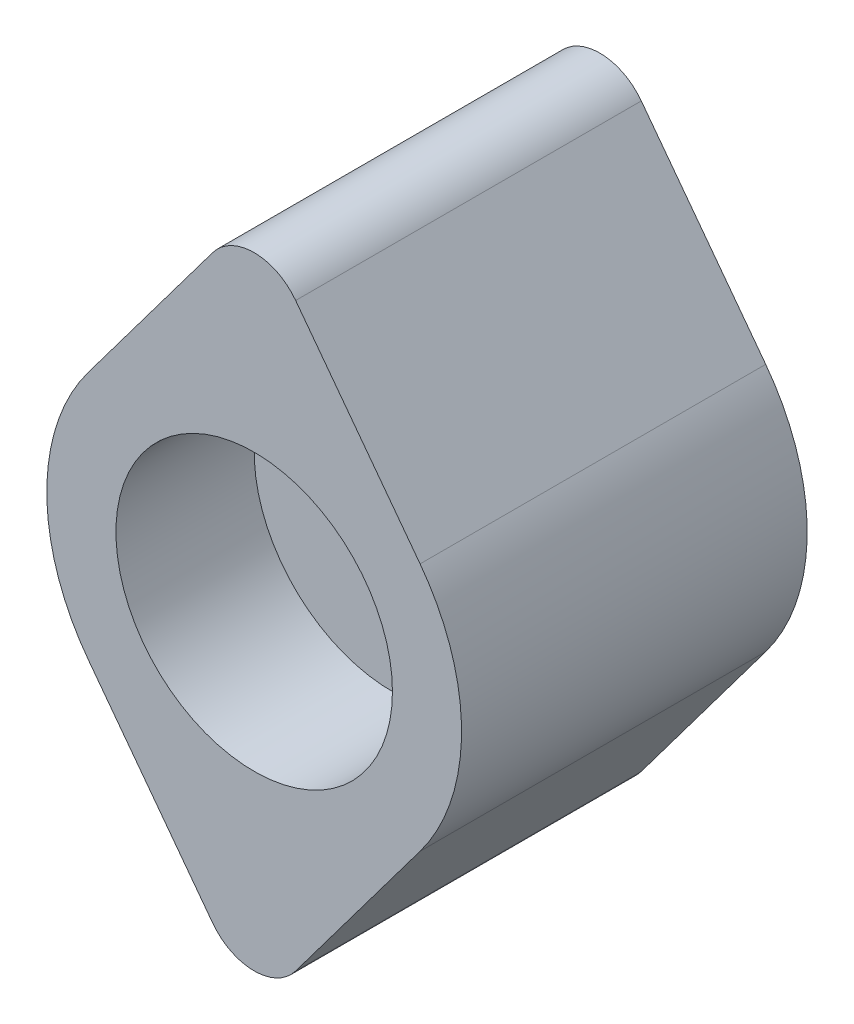
SolidWorks part; units mm, degrees
ref_plane "Спереди" through (0, 0, 0) normal (0, 0, 1) x (1, 0, 0)
ref_plane "Сверху" through (0, 0, 0) normal (0, 1, 0) x (1, 0, 0)
ref_plane "Справа" through (0, 0, 0) normal (1, 0, 0) x (0, 0, -1)
sketch "Эскиз1" plane through (0, 0, 0) normal (0, 0, 1) x (1, 0, 0)
  line L0 (0, 43.4129) -> (0, -56.9191) construction
  line L1 (-52.9224, 0) -> (49.3391, 0) construction
  line L2 (-18.0003, 10) -> (26.0336, 10) construction
  line L3 (-15.5369, -10) -> (30.1599, -10) construction
  line L4 (0, 10) -> (-4.8, 3.6)
  line L5 (0, 10) -> (4.8, 3.6)
  line L6 (0, -10) -> (4.8, -3.6)
  line L7 (0, -10) -> (-4.8, -3.6)
  arc A0 (-4.8, 3.6) -> (-4.8, -3.6) centre (0, 0) ccw
  arc A1 (4.8, -3.6) -> (4.8, 3.6) centre (0, 0) ccw
  dimension "D1" = 12
  dimension "D2" = 10
  dimension "D3" = 10
extrude "Бобышка-Вытянуть1" add sketch "Эскиз1" along normal blind 10
sketch "Эскиз2" plane through (0, 0, 10) normal (0, 0, 1) x (1, 0, 0)
  circle A0 centre (0, 0) radius 4
  dimension "D1" = 8
extrude "Вырез-Вытянуть1" cut sketch "Эскиз2" against normal blind 4
hole_wizard "Отверстие обработанное метчиком M4x0.71" positions "Эскиз4" profile "Эскиз3" tap size "M4x0.7" standard "Ansi Metric" end condition through all
sketch "Эскиз4" plane through (0, 0, 6) normal (0, 0, 1) x (1, 0, 0)
  point P0 (0, 0)
sketch "Эскиз3" plane through (0, 0, 6) normal (1, 0, 0) x (0, -1, 0)
  line L0 (0, 0) -> (0, 6)
  line L1 (0, 6) -> (1.65, 6)
  line L2 (1.65, 6) -> (1.65, 0)
  line L5 (1.65, 0) -> (0, 0)
  line L11 (0, -6.35) -> (0, 107.95) construction
  dimension "Диаметр проходного сверла" = 3.3
  dimension "Глубина проходного сверла" = 6
cosmetic thread "Отверстие резьбы1" parameters "D2"=4
fillet "Скругление1" radius 1.5 2 edges at (0, -10, 5) (0, 10, 5)
